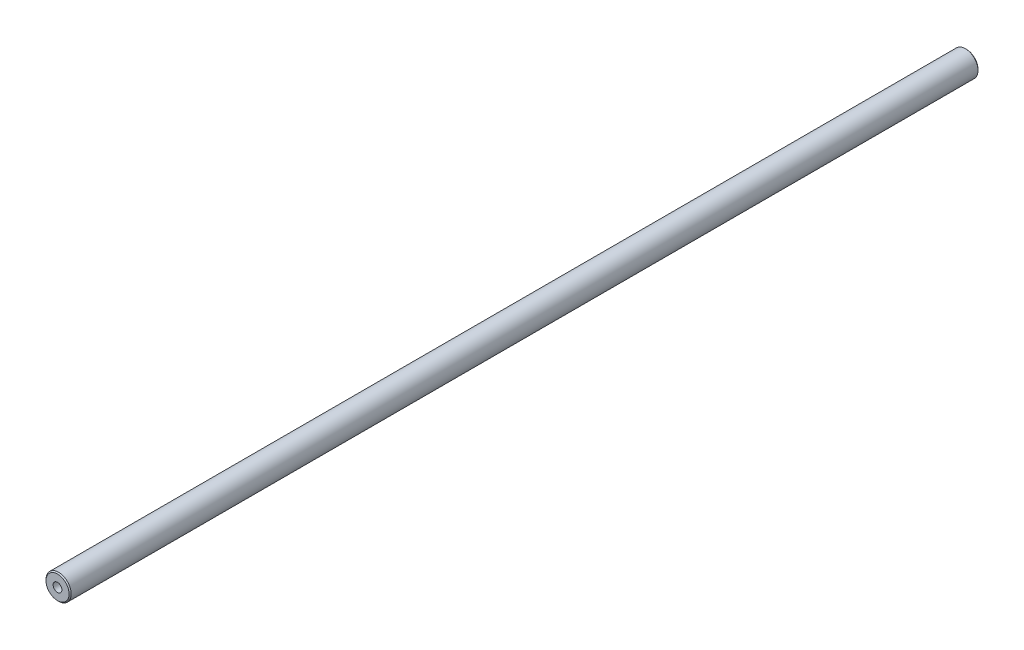
SolidWorks part; units mm, degrees
material "Alloy Steel"
ref_plane "Front Plane" through (0, 0, 0) normal (0, 0, 1) x (1, 0, 0)
ref_plane "Top Plane" through (0, 0, 0) normal (0, 1, 0) x (1, 0, 0)
ref_plane "Right Plane" through (0, 0, 0) normal (1, 0, 0) x (0, 0, -1)
sketch "Sketch1" plane through (0, 0, 0) normal (0, 0, 1) x (1, 0, 0)
  circle A0 centre (0, 0) radius 6
  dimension "D1" = 12
extrude "Boss-Extrude1" add sketch "Sketch1" along normal up to surface (433.4811 mm away)
chamfer "Chamfer1" distance 0.5 angle 45 2 edges at (6, 0, 0) (0, -6, 433.4811)
hole_wizard "M5x0.8 Tapped Hole1" positions "3DSketch1" profile "Sketch3" tap size "M5x0.8" standard "ANSI Metric"
sketch3d "3DSketch1"
  line L0 (0, 0, 432.9811) -> (0, 0, 433.4811) construction
  line L1 (0, 0, 0.5) -> (0, 0, 0) construction
  point P0 (0, 0, 433.4811)
  point P4 (0, 0, 0)
sketch "Sketch3" plane through (0, 0, 433.4811) normal (1, 0, 0) x (0, -1, 0)
  line L0 (0, 0) -> (0, 17.6618)
  line L1 (0, 17.6618) -> (2.1, 16.4)
  line L2 (2.1, 16.4) -> (2.1, 0)
  line L5 (2.1, 0) -> (0, 0)
  line L10 (0, 17.6618) -> (-2.1, 16.4) construction
  line L11 (0, -6.35) -> (0, 107.95) construction
  dimension "Tap Drill Dia." = 4.2
  dimension "Tap Drill Depth" = 16.4
  dimension "Drill Angle" = 118
cosmetic thread "Hole Thread1" parameters "D1"=14, "D2"=5
cosmetic thread "Hole Thread2" parameters "D1"=14, "D2"=5
